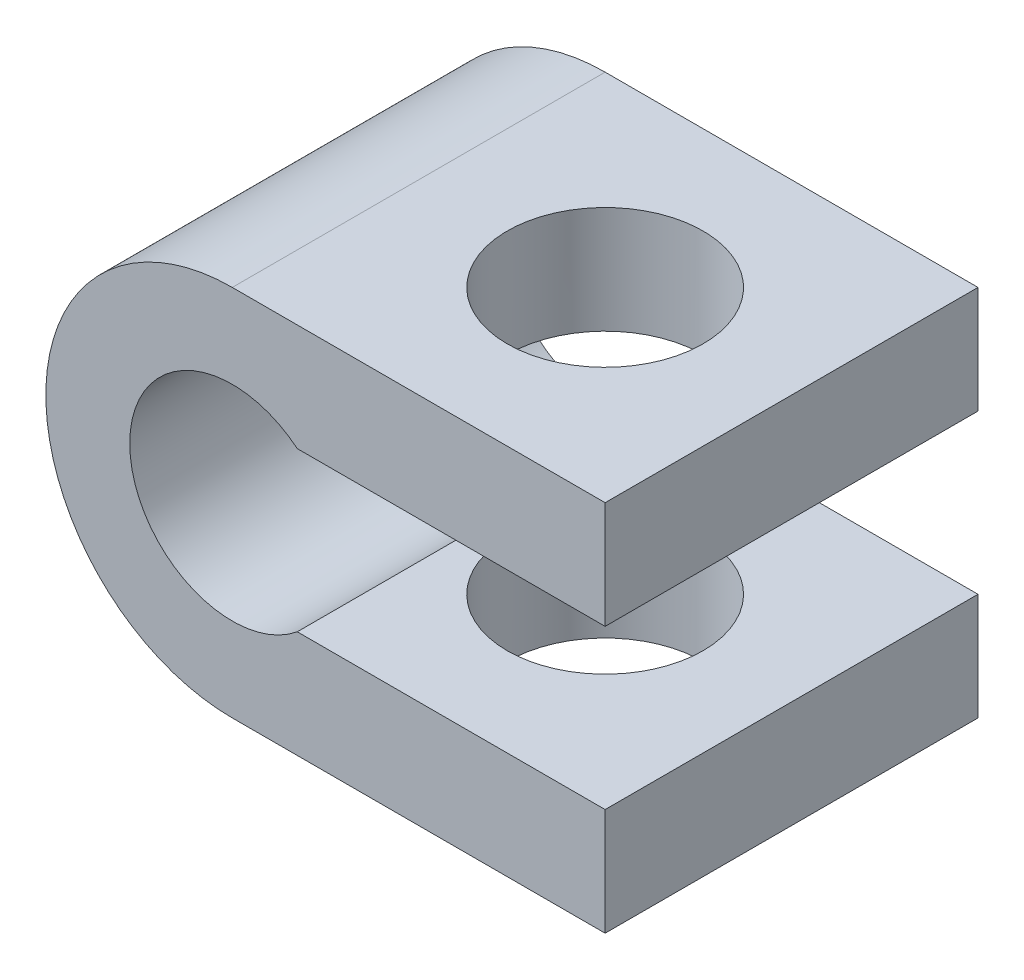
SolidWorks part; units mm, degrees
ref_plane "Front Plane" through (0, 0, 0) normal (0, 0, 1) x (1, 0, 0)
ref_plane "Top Plane" through (0, 0, 0) normal (0, 1, 0) x (1, 0, 0)
ref_plane "Right Plane" through (0, 0, 0) normal (1, 0, 0) x (0, 0, -1)
sketch "Sketch1" plane through (0, 0, 0) normal (0, 0, 1) x (1, 0, 0)
  line L0 (0, 6) -> (12, 6)
  line L1 (12, 6) -> (12, 2.5527)
  line L2 (12, 2.5527) -> (2.0913, 2.5527)
  line L3 (-11.5353, 0) -> (18.1518, 0) construction
  line L4 (12, -2.5527) -> (2.0913, -2.5527)
  line L5 (12, -6) -> (12, -2.5527)
  line L6 (0, -6) -> (12, -6)
  arc A0 (2.0913, 2.5527) -> (2.0913, -2.5527) centre (0, 0) ccw
  arc A2 (0, 6) -> (0, -6) centre (0, 0) ccw
  dimension "D1" = 3.3
  dimension "D2" = 6
  dimension "D3" = 12
  dimension "D4" = 5.1054
extrude "Boss-Extrude1" add sketch "Sketch1" along normal blind 12
sketch "Sketch2" plane through (0, 0, 0) normal (0, 1, 0) x (1, 0, 0)
  circle A0 centre (6, -6) radius 3.15
  dimension "D3" = 6.3
  dimension "D1" = 6
  dimension "D2" = 6
extrude "Cut-Extrude1" cut sketch "Sketch2" against normal through all and the other way through all
